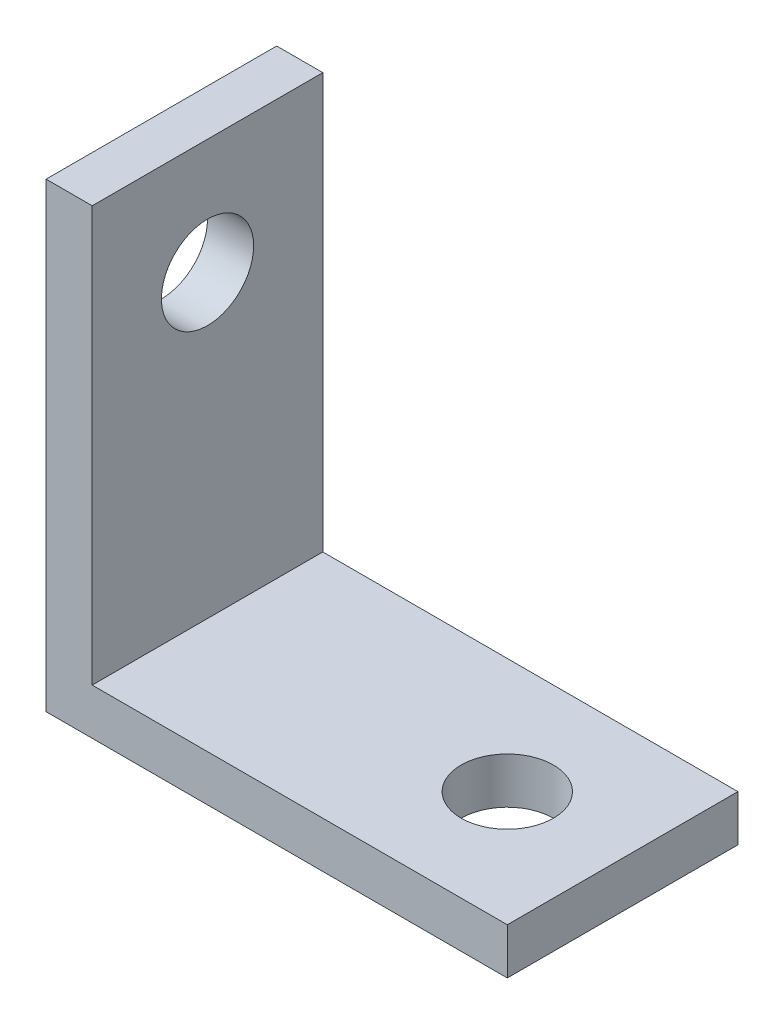
SolidWorks part; units mm, degrees
ref_plane "Front Plane" through (0, 0, 0) normal (0, 0, 1) x (1, 0, 0)
ref_plane "Top Plane" through (0, 0, 0) normal (0, 1, 0) x (1, 0, 0)
ref_plane "Right Plane" through (0, 0, 0) normal (1, 0, 0) x (0, 0, -1)
sketch "Sketch1" plane through (0, 0, 0) normal (0, 0, 1) x (1, 0, 0)
  line L2 (-7.8406, 0) -> (-7.8406, 20)
  line L3 (-7.8406, 20) -> (-9.8406, 20)
  line L4 (-9.8406, 0) -> (-9.8406, 20)
  line L5 (-9.8406, 2) -> (10.1594, 2)
  line L7 (-9.8406, 0) -> (10.1594, 0)
  line L8 (10.1594, 2) -> (10.1594, 0)
  dimension "D1" = 2
  dimension "D2" = 2
  dimension "D3" = 20
  dimension "D4" = 20
extrude "Boss-Extrude2" add sketch "Sketch1" along normal blind 10 contours L4 L5 L2 L3 | L4 L7 L2 L5 | L8 L5 L2 L7
sketch "Sketch3" plane through (0, 2, 0) normal (0, 1, 0) x (1, 0, 0)
  line L0 (10.1594, -10) -> (10.1594, 0) construction
  line L1 (-7.8406, 0) -> (10.1594, 0) construction
  circle A0 centre (5.1594, -5) radius 2
  dimension "D1" = 4
  dimension "D2" = 5
  dimension "D3" = 5
extrude "Cut-Extrude1" cut sketch "Sketch3" against normal through all
sketch "Sketch4" plane through (-7.8406, 0, 0) normal (1, 0, 0) x (0, 0, -1)
  line L0 (-10, 2) -> (-10, 20) construction
  line L1 (-10, 20) -> (0, 20) construction
  circle A0 centre (-5, 15) radius 2
  dimension "D1" = 4
  dimension "D2" = 5
  dimension "D3" = 5
extrude "Cut-Extrude2" cut sketch "Sketch4" against normal through all
